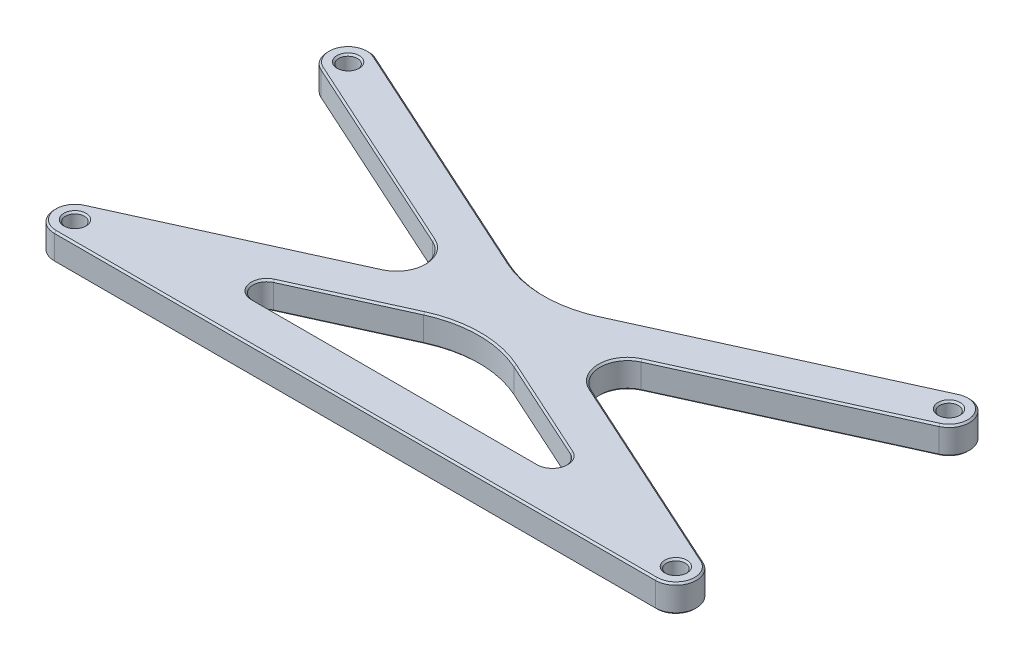
SolidWorks part; units mm, degrees
ref_plane "Front Plane" through (0, 0, 0) normal (0, 0, 1) x (1, 0, 0)
ref_plane "Top Plane" through (0, 0, 0) normal (0, 1, 0) x (1, 0, 0)
ref_plane "Right Plane" through (0, 0, 0) normal (1, 0, 0) x (0, 0, -1)
sketch "Sketch1" plane through (0, 0, 0) normal (0, 1, 0) x (1, 0, 0)
  line L0 (-69.85, -4.7625) -> (69.85, -4.7625)
  line L1 (-47.8634, 4.7625) -> (47.8634, 4.7625)
  line L2 (-71.8207, 4.3356) -> (-11.5091, 31.75)
  line L3 (71.8207, 59.1644) -> (11.5091, 31.75)
  line L4 (-67.8793, 67.8356) -> (0, 36.9814)
  line L5 (-71.8207, 59.1644) -> (-11.5091, 31.75)
  line L6 (0, 36.9814) -> (67.8793, 67.8356)
  line L7 (0, 26.5186) -> (-47.8634, 4.7625)
  line L8 (11.5091, 31.75) -> (71.8207, 4.3356)
  line L9 (0, 26.5186) -> (47.8634, 4.7625)
  circle A0 centre (-69.85, 0) radius 2.1828
  circle A1 centre (69.85, 0) radius 2.1828
  circle A2 centre (-69.85, 63.5) radius 2.1828
  circle A3 centre (69.85, 63.5) radius 2.1828
  arc A4 (-67.8793, 67.8356) -> (-71.8207, 59.1644) centre (-69.85, 63.5) ccw
  arc A5 (-71.8207, 4.3356) -> (-69.85, -4.7625) centre (-69.85, 0) ccw
  arc A6 (69.85, -4.7625) -> (71.8207, 4.3356) centre (69.85, 0) ccw
  arc A7 (71.8207, 59.1644) -> (67.8793, 67.8356) centre (69.85, 63.5) ccw
  point P7 (0, 0)
  dimension "D3" = 4.3656
  dimension "D4" = 4.3656
  dimension "D6" = 4.3656
  dimension "D7" = 4.3656
  dimension "D8" = 9.525
  dimension "D9" = 9.525
  dimension "D10" = 9.525
  dimension "D11" = 9.525
  dimension "D1" = 69.85
  dimension "D2" = 69.85
  dimension "D5" = 63.5
extrude "Boss-Extrude1" add sketch "Sketch1" along normal blind 6.35
fillet "Fillet1" radius 25.4 2 edges at (0, 3.175, -26.5186) (0, 3.175, -36.9814)
fillet "Fillet2" radius 3.175 2 edges at (47.8634, 3.175, -4.7625) (-47.8634, 3.175, -4.7625)
fillet "Fillet3" radius 6.35 2 edges at (-11.5091, 3.175, -31.75) (11.5091, 3.175, -31.75)
chamfer "Chamfer1" distance 0.3969 angle 45 48 edges at (-36.3087, 0, -7.2654) (-22.515, 0, -16.2845) (0, 0, -24.0177) (22.515, 0, -16.2845) (36.3087, 0, -7.2654) (0, 0, -4.7625) (0, 0, 4.7625) (74.5046, 0, 1.0082) (48.0238, 0, -15.1524) (20.5046, 0, -31.75) (48.0238, 0, -48.3476) (74.1856, 0, -65.4707) (39.1949, 0, -54.7973) (0, 0, -39.4823) (-39.1949, 0, -54.7973) (-74.1856, 0, -65.4707) (-48.0238, 0, -48.3476) (-20.5046, 0, -31.75) (-48.0238, 0, -15.1524) (-74.5046, 0, 1.0082) (-69.85, 0, 2.1828) (69.85, 0, 2.1828) (69.85, 0, -61.3172) (-69.85, 0, -61.3172) (-36.3087, 6.35, -7.2654) (0, 6.35, -4.7625) (36.3087, 6.35, -7.2654) (22.515, 6.35, -16.2845) (0, 6.35, -24.0177) (-22.515, 6.35, -16.2845) (-69.85, 6.35, -61.3172) (69.85, 6.35, 2.1828) (-48.0238, 6.35, -15.1524) (-20.5046, 6.35, -31.75) (-48.0238, 6.35, -48.3476) (-74.1856, 6.35, -65.4707) (-39.1949, 6.35, -54.7973) (0, 6.35, -39.4823) (39.1949, 6.35, -54.7973) (74.1856, 6.35, -65.4707) (48.0238, 6.35, -48.3476) (20.5046, 6.35, -31.75) (48.0238, 6.35, -15.1524) (74.5046, 6.35, 1.0082) (0, 6.35, 4.7625) (-74.5046, 6.35, 1.0082) (-69.85, 6.35, 2.1828) (69.85, 6.35, -61.3172)
